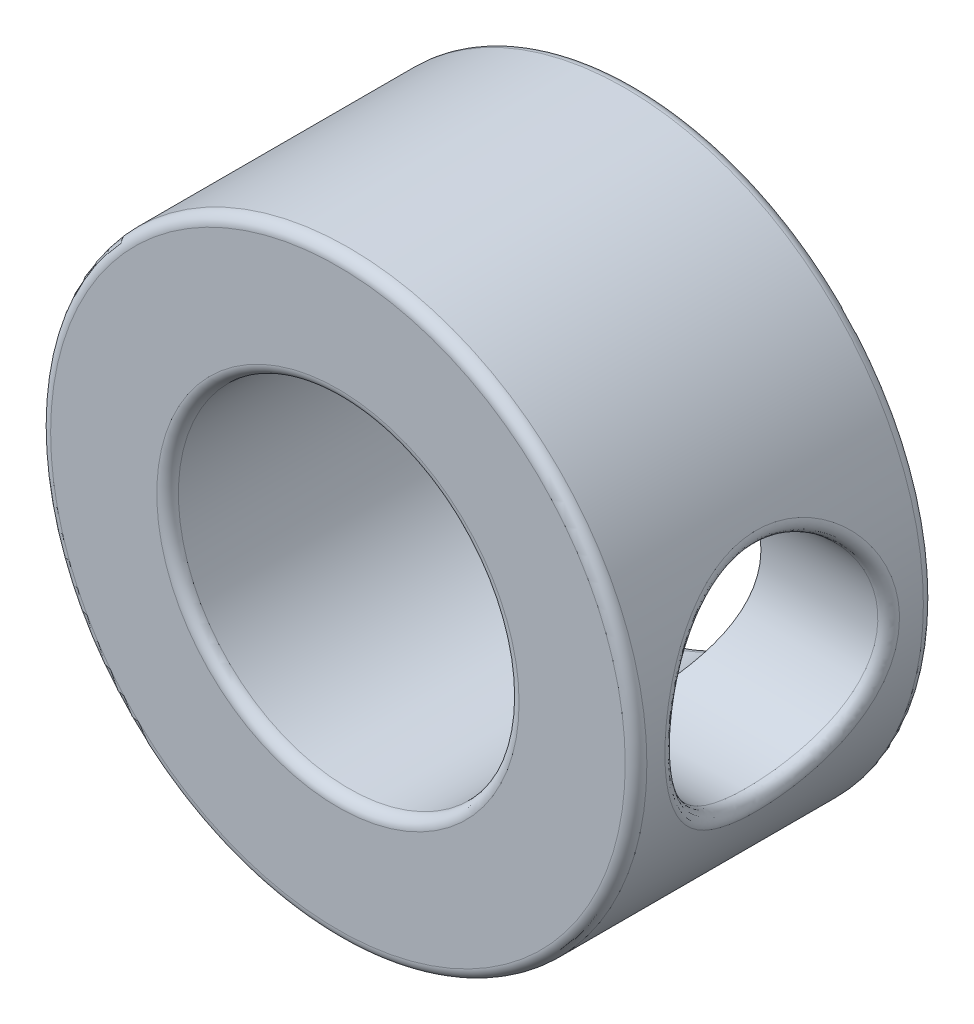
SolidWorks part; units mm, degrees
material "Chrome Stainless Steel"
ref_plane "Front Plane" through (0, 0, 0) normal (0, 0, 1) x (1, 0, 0)
ref_plane "Top Plane" through (0, 0, 0) normal (0, 1, 0) x (1, 0, 0)
ref_plane "Right Plane" through (0, 0, 0) normal (1, 0, 0) x (0, 0, -1)
sketch "Sketch2" plane through (0, 0, 0) normal (0, 0, 1) x (1, 0, 0)
  circle A0 centre (0, 0) radius 7
  dimension "D1" = 14
extrude "Boss-Extrude1" add sketch "Sketch2" along normal blind 7
sketch "Sketch3" plane through (0, 0, 7) normal (0, 0, 1) x (1, 0, 0)
  circle A0 centre (0, 0) radius 4
  dimension "D1" = 8
extrude "Cut-Extrude1" cut sketch "Sketch3" against normal through all contours A0
sketch "Sketch4" plane through (0, 0, 0) normal (1, 0, 0) x (0, 0, -1)
  circle A0 centre (-3.5687, 0) radius 2.5
  dimension "D1" = 5
  dimension "D2" = 3.5687
extrude "Cut-Extrude2" cut sketch "Sketch4" along normal through all
fillet "Fillet1" radius 0.254 5 edges at (4, 0, 0) (7, 0, 0) (6.9884, 0.4037, 1.1015) (4, 0, 7) (7, 0, 7)
